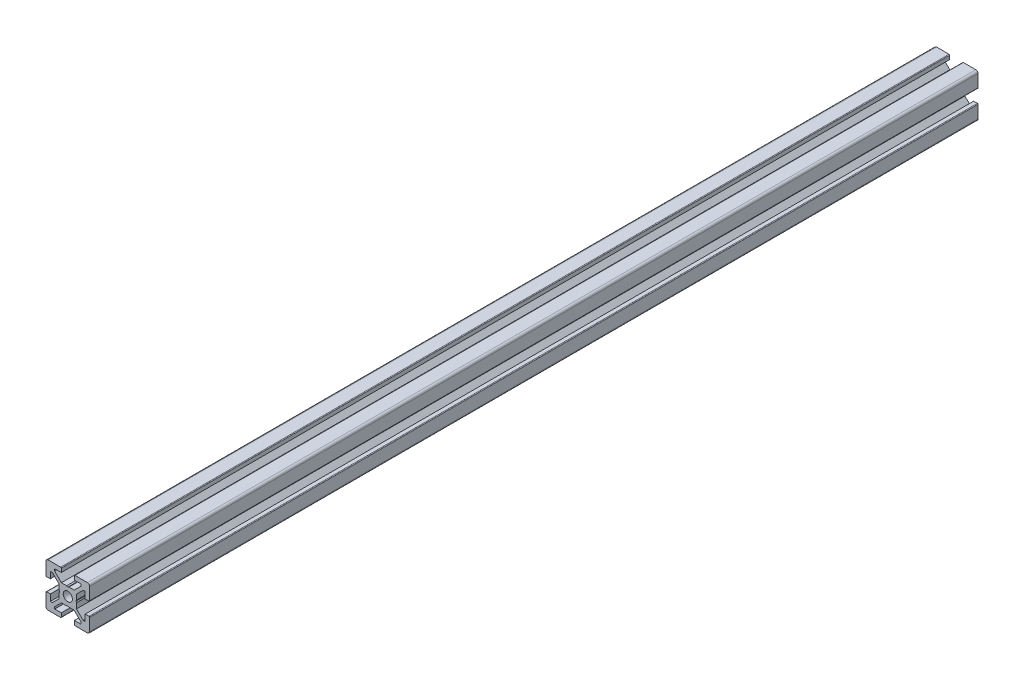
SolidWorks part; units mm, degrees
material "6063-T5"
ref_plane "Front Plane" through (0, 0, 0) normal (0, 0, 1) x (1, 0, 0)
ref_plane "Top Plane" through (0, 0, 0) normal (0, 1, 0) x (1, 0, 0)
ref_plane "Right Plane" through (0, 0, 0) normal (1, 0, 0) x (0, 0, -1)
ref_plane "Plane1" through (0, 0, 0) normal (0, 0, 1) x (1, 0, 0)
sketch "Sketch1" plane through (0, 0, 0) normal (0, 0, 1) x (1, 0, 0)
  line L0 (-10, 9) -> (-10, 3.3)
  line L1 (-9.7, 3) -> (-8, 3)
  line L2 (-8, 3) -> (-8, 6)
  line L3 (-8, 6) -> (-7.0607, 6)
  line L4 (-7.0607, 6) -> (-4, 2.9393)
  line L5 (-4, 2.9393) -> (-4, 0.5196)
  line L6 (-4, 0.5196) -> (-3.7, 0)
  line L7 (-3.7, 0) -> (-4, -0.5196)
  line L8 (-4, -0.5196) -> (-4, -2.9393)
  line L9 (-4, -2.9393) -> (-7.0607, -6)
  line L10 (-7.0607, -6) -> (-8, -6)
  line L11 (-8, -6) -> (-8, -3)
  line L12 (-8, -3) -> (-9.7, -3)
  line L13 (-10, -3.3) -> (-10, -9)
  line L14 (-9, -10) -> (-3.3, -10)
  line L15 (-3, -9.7) -> (-3, -8)
  line L16 (-3, -8) -> (-6, -8)
  line L17 (-6, -8) -> (-6, -7.0607)
  line L18 (-6, -7.0607) -> (-2.9393, -4)
  line L19 (-2.9393, -4) -> (-0.5196, -4)
  line L20 (-0.5196, -4) -> (0, -3.7)
  line L21 (0, -3.7) -> (0.5196, -4)
  line L22 (0.5196, -4) -> (2.9393, -4)
  line L23 (2.9393, -4) -> (6, -7.0607)
  line L24 (6, -7.0607) -> (6, -8)
  line L25 (6, -8) -> (3, -8)
  line L26 (3, -8) -> (3, -9.7)
  line L27 (3.3, -10) -> (9, -10)
  line L28 (10, -9) -> (10, -3.3)
  line L29 (9.7, -3) -> (8, -3)
  line L30 (8, -3) -> (8, -6)
  line L31 (8, -6) -> (7.0606, -6)
  line L32 (7.0606, -6) -> (4, -2.9393)
  line L33 (4, -2.9393) -> (4, -0.5196)
  line L34 (4, -0.5196) -> (3.7, 0)
  line L35 (3.7, 0) -> (4, 0.5196)
  line L36 (4, 0.5196) -> (4, 2.9393)
  line L37 (4, 2.9393) -> (7.0607, 6)
  line L38 (7.0607, 6) -> (8, 6)
  line L39 (8, 6) -> (8, 3)
  line L40 (8, 3) -> (9.7, 3)
  line L41 (10, 3.3) -> (10, 9)
  line L42 (9, 10) -> (3.3, 10)
  line L43 (3, 9.7) -> (3, 8)
  line L44 (3, 8) -> (6, 8)
  line L45 (6, 8) -> (6, 7.0607)
  line L46 (6, 7.0607) -> (2.9393, 4)
  line L47 (2.9393, 4) -> (0.5196, 4)
  line L48 (0.5196, 4) -> (0, 3.7)
  line L49 (0, 3.7) -> (-0.5196, 4)
  line L50 (-0.5196, 4) -> (-2.9394, 4)
  line L51 (-2.9394, 4) -> (-6, 7.0606)
  line L52 (-6, 7.0606) -> (-6, 8)
  line L53 (-6, 8) -> (-3, 8)
  line L54 (-3, 8) -> (-3, 9.7)
  line L55 (-3.3, 10) -> (-9, 10)
  arc A0 (-10, 3.3) -> (-9.7, 3) centre (-9.7, 3.3) ccw
  arc A1 (-9.7, -3) -> (-10, -3.3) centre (-9.7, -3.3) ccw
  arc A2 (-10, -9) -> (-9, -10) centre (-9, -9) ccw
  arc A3 (-3.3, -10) -> (-3, -9.7) centre (-3.3, -9.7) ccw
  arc A4 (3, -9.7) -> (3.3, -10) centre (3.3, -9.7) ccw
  arc A5 (9, -10) -> (10, -9) centre (9, -9) ccw
  arc A6 (10, -3.3) -> (9.7, -3) centre (9.7, -3.3) ccw
  arc A7 (9.7, 3) -> (10, 3.3) centre (9.7, 3.3) ccw
  arc A8 (10, 9) -> (9, 10) centre (9, 9) ccw
  arc A9 (3.3, 10) -> (3, 9.7) centre (3.3, 9.7) ccw
  arc A10 (-3, 9.7) -> (-3.3, 10) centre (-3.3, 9.7) ccw
  arc A11 (-9, 10) -> (-10, 9) centre (-9, 9) ccw
extrude "Boss-Extrude1" add sketch "Sketch1" against normal blind 407.5
ref_plane "Plane2" through (0, 0, 0) normal (1, 0, 0) x (0, 0, -1)
sketch "Sketch2" plane through (0, 0, 0) normal (1, 0, 0) x (0, 0, -1)
  line L0 (0, 0) -> (0, 2.1)
  line L1 (0, 2.1) -> (407.5, 2.1)
  line L2 (407.5, 2.1) -> (407.5, 0)
  line L3 (407.5, 0) -> (0, 0)
  line L4 (407.5, 0) -> (0, 0) construction
  dimension "D1" = 2.1
  dimension "D2" = 407.5
revolve "Cut-Revolve1" cut sketch "Sketch2" angle 360 about L4
ref_plane "Plane3" through (0, 0, -203.75) normal (0, 0, 1) x (1, 0, 0)
sketch "Sketch4" plane through (4, 0, 0) normal (1, 0, 0) x (0, 0, -1)
  line L0 (407.5, 0) -> (0, 0) construction
  line L1 (0, -2.9393) -> (0, -0.5196) construction
  line L2 (203.75, 2.9393) -> (203.75, -2.9393) construction
  line L3 (407.5, 2.9393) -> (0, 2.9393) construction
  line L4 (407.5, -2.9393) -> (0, -2.9393) construction
  circle A0 centre (10, 0) radius 2.5
  circle A1 centre (397.5, 0) radius 2.5
  dimension "D1" = 5
  dimension "D2" = 10
extrude "Cut-Extrude1" [suppressed] cut sketch "Sketch4" against normal up to surface (8 mm away)
